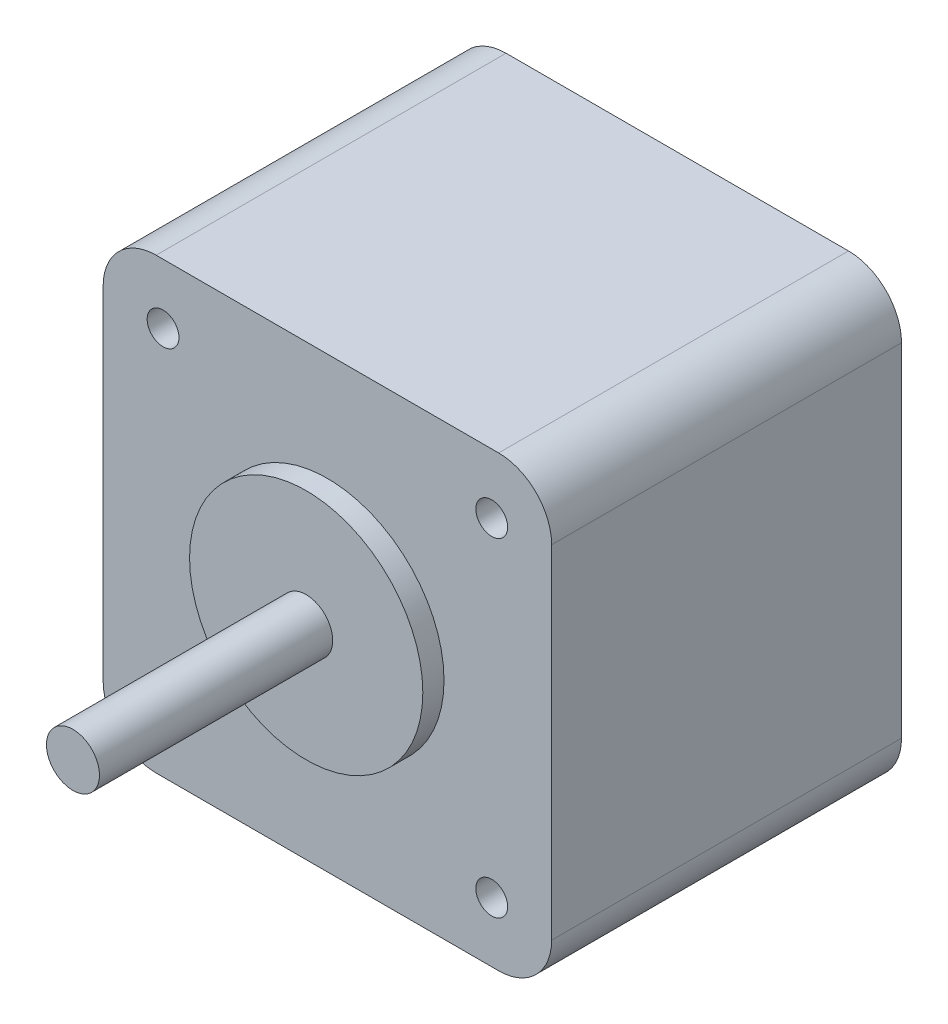
SolidWorks part; units mm, degrees
ref_plane "Front Plane" through (0, 0, 0) normal (0, 0, 1) x (1, 0, 0)
ref_plane "Top Plane" through (0, 0, 0) normal (0, 1, 0) x (1, 0, 0)
ref_plane "Right Plane" through (0, 0, 0) normal (1, 0, 0) x (0, 0, -1)
sketch "Sketch1" plane through (0, 0, 0) normal (0, 0, 1) x (1, 0, 0)
  line L1 (-16.15, -21.15) -> (16.15, -21.15)
  line L2 (-21.15, -16.15) -> (-21.15, 16.15)
  line L3 (-16.15, 21.15) -> (16.15, 21.15)
  line L4 (21.15, -16.15) -> (21.15, 16.15)
  line L5 (-21.15, -21.15) -> (21.15, 21.15) construction
  line L6 (-21.15, 21.15) -> (21.15, -21.15) construction
  line L11 (-23.57, -23.57) -> (23.57, 23.57) construction
  line L12 (-23.57, 23.57) -> (23.57, -23.57) construction
  arc A0 (-16.15, -21.15) -> (-21.15, -16.15) centre (-16.15, -16.15) cw
  arc A1 (16.15, -21.15) -> (21.15, -16.15) centre (16.15, -16.15) ccw
  arc A2 (16.15, 21.15) -> (21.15, 16.15) centre (16.15, 16.15) cw
  arc A3 (-16.15, 21.15) -> (-21.15, 16.15) centre (-16.15, 16.15) ccw
  point P0 (0, 0)
  point P18 (0, 0)
  dimension "D3" = 5
  dimension "D1" = 42.3
  dimension "D2" = 42.3
extrude "Boss-Extrude1" add sketch "Sketch1" along normal mid plane 33
sketch "Sketch5" plane through (0, 0, 16.5) normal (0, 0, 1) x (1, 0, 0)
  line L1 (-15.5, -15.5) -> (15.5, -15.5) construction
  line L2 (-15.5, -15.5) -> (-15.5, 15.5) construction
  line L3 (-15.5, 15.5) -> (15.5, 15.5) construction
  line L4 (15.5, -15.5) -> (15.5, 15.5) construction
  line L5 (-15.5, -15.5) -> (15.5, 15.5) construction
  line L6 (-15.5, 15.5) -> (15.5, -15.5) construction
  circle A0 centre (-15.5, 15.5) radius 1.5
  circle A1 centre (15.5, 15.5) radius 1.5
  circle A2 centre (15.5, -15.5) radius 1.5
  circle A3 centre (-15.5, -15.5) radius 1.5
  point P0 (0, 0)
  dimension "D3" = 3
  dimension "D4" = 3
  dimension "D5" = 3
  dimension "D6" = 3
  dimension "D1" = 31
  dimension "D2" = 31
extrude "Cut-Extrude1" cut sketch "Sketch5" against normal through all
sketch "Sketch2" plane through (0, 0, 16.5) normal (0, 0, 1) x (1, 0, 0)
  circle A0 centre (0, 0) radius 2.5
  dimension "D1" = 5
extrude "Boss-Extrude2" add sketch "Sketch2" along normal blind 24
sketch "Sketch3" plane through (0, 0, 16.5) normal (0, 0, 1) x (1, 0, 0)
  circle A0 centre (0, 0) radius 11
  dimension "D1" = 22
extrude "Boss-Extrude3" add sketch "Sketch3" along normal blind 2
